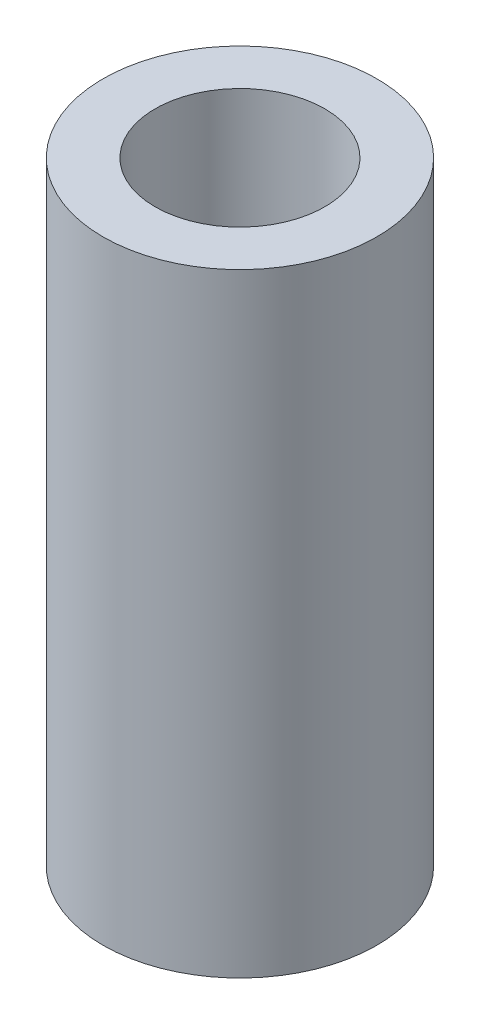
SolidWorks part; units mm, degrees
ref_plane "Face" through (0, 0, 0) normal (0, 0, 1) x (1, 0, 0)
ref_plane "Dessus" through (0, 0, 0) normal (0, 1, 0) x (1, 0, 0)
ref_plane "Droite" through (0, 0, 0) normal (1, 0, 0) x (0, 0, -1)
sketch "Esquisse1" plane through (0, 0, 0) normal (0, 1, 0) x (1, 0, 0)
  circle A0 centre (0, 0) radius 12.5
  circle A1 centre (0, 0) radius 7.75
  dimension "D1" = 25
  dimension "D2" = 15.5
extrude "Extrusion1" add sketch "Esquisse1" along normal blind 56
